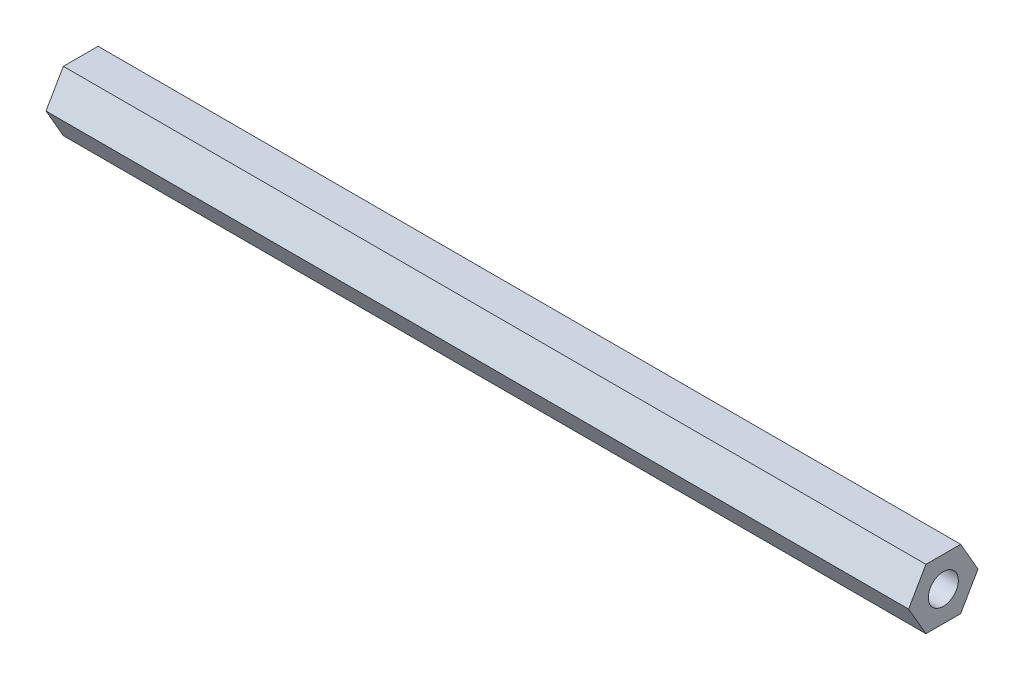
SolidWorks part; units mm, degrees
material "6061-T6 (SS)"
ref_plane "Front" through (0, 0, 0) normal (0, 0, 1) x (1, 0, 0)
ref_plane "Top" through (0, 0, 0) normal (0, 1, 0) x (1, 0, 0)
ref_plane "Right" through (0, 0, 0) normal (1, 0, 0) x (0, 0, -1)
sketch "Sketch1" plane through (0, 0, 0) normal (1, 0, 0) x (0, 0, -1)
  line L1 (1.4434, 2.5) -> (-1.4434, 2.5)
  line L2 (-1.4434, 2.5) -> (-2.8868, 0)
  line L3 (-2.8868, 0) -> (-1.4434, -2.5)
  line L4 (-1.4434, -2.5) -> (1.4434, -2.5)
  line L5 (1.4434, -2.5) -> (2.8868, 0)
  line L6 (2.8868, 0) -> (1.4434, 2.5)
  circle A0 centre (0, 0) radius 2.5 construction
  dimension "D1" = 5
extrude "Boss-Extrude1" add sketch "Sketch1" along normal blind 71.755
sketch "Sketch6" plane through (0, 0, 0) normal (-1, 0, 0) x (0, 0, 1)
  point P0 (0, 0)
hole_wizard "M3x0.5 Tapped Hole1" positions "Sketch6" profile "Sketch5" tap size "M3x0.5" standard "ANSI Metric"
sketch "Sketch5" plane through (0, 0, 0) normal (0, 1, 0) x (0, 0, 1)
  line L0 (0, 0) -> (0, 8.2441)
  line L1 (0, 8.2441) -> (1.25, 7.493)
  line L2 (1.25, 7.493) -> (1.25, 0)
  line L5 (1.25, 0) -> (0, 0)
  line L10 (0, 8.2441) -> (-1.25, 7.493) construction
  line L11 (0, -6.35) -> (0, 107.95) construction
  dimension "Tap Drill Dia." = 2.5
  dimension "Tap Drill Depth" = 7.493
  dimension "Drill Angle" = 118
cosmetic thread "Hole Thread1" parameters "D1"=5.9944, "D2"=3
sketch "Sketch9" plane through (71.755, 0, 0) normal (1, 0, 0) x (0, 0, -1)
  point P0 (0, 0)
hole_wizard "M3x0.5 Tapped Hole2" positions "Sketch9" profile "Sketch8" tap size "M3x0.5" standard "ANSI Metric"
sketch "Sketch8" plane through (71.755, 0, 0) normal (0, 1, 0) x (0, 0, -1)
  line L0 (0, 0) -> (0, 8.2441)
  line L1 (0, 8.2441) -> (1.25, 7.493)
  line L2 (1.25, 7.493) -> (1.25, 0)
  line L5 (1.25, 0) -> (0, 0)
  line L10 (0, 8.2441) -> (-1.25, 7.493) construction
  line L11 (0, -6.35) -> (0, 107.95) construction
  dimension "Tap Drill Dia." = 2.5
  dimension "Tap Drill Depth" = 7.493
  dimension "Drill Angle" = 118
cosmetic thread "Hole Thread2" parameters "D1"=5.9944, "D2"=3
